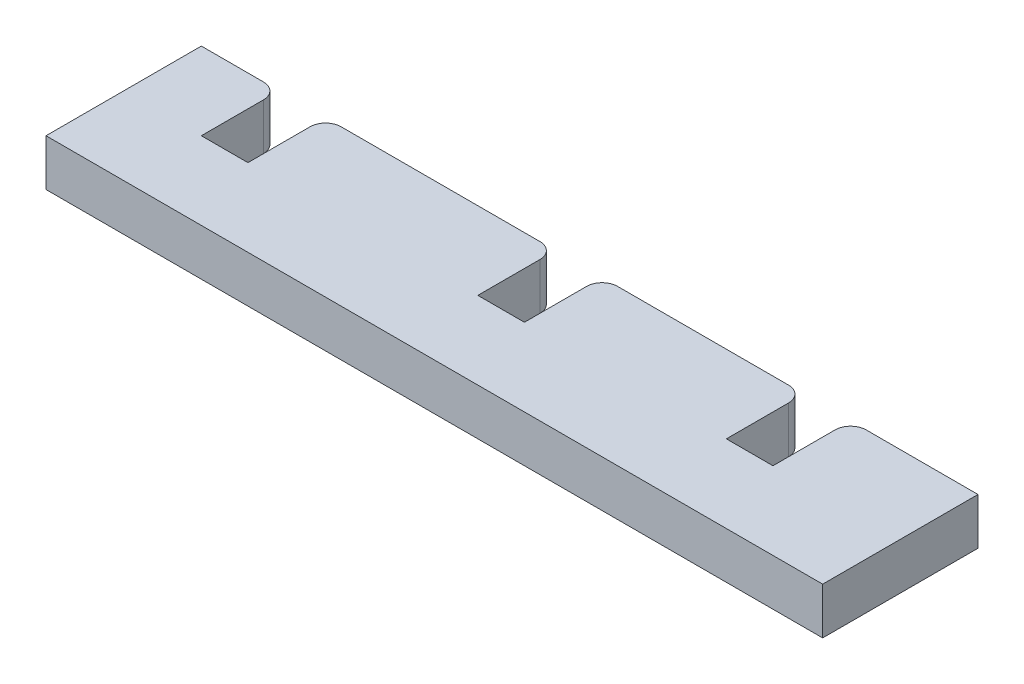
SolidWorks part; units mm, degrees
ref_plane "Front Plane" through (0, 0, 0) normal (0, 0, 1) x (1, 0, 0)
ref_plane "Top Plane" through (0, 0, 0) normal (0, 1, 0) x (1, 0, 0)
ref_plane "Right Plane" through (0, 0, 0) normal (1, 0, 0) x (0, 0, -1)
sketch "Sketch1" plane through (0, 0, 0) normal (0, 0, 1) x (1, 0, 0)
  line L1 (0, 0) -> (50, 0)
  line L2 (0, 0) -> (0, 3)
  line L3 (0, 3) -> (50, 3)
  line L4 (50, 0) -> (50, 3)
  dimension "D1" = 3
  dimension "D2" = 50
extrude "Boss-Extrude1" add sketch "Sketch1" along normal blind 10
sketch "Sketch3" plane through (0, 0, 0) normal (0, 0, -1) x (-1, 0, 0)
  line L0 (0, 0) -> (-50, 0) construction
  line L4 (-82.8, 3) -> (-82.8, 0)
  line L5 (-50, 3) -> (0, 3) construction
  line L7 (-79.8, 3) -> (-79.8, 0)
  line L9 (-61.8, 3) -> (-61.8, 0)
  line L10 (-82.8, 3) -> (-79.8, 3)
  line L12 (-58.8, 3) -> (-58.8, 0)
  line L14 (-41.8, 3) -> (-41.8, 0)
  line L16 (-38.8, 3) -> (-38.8, 0)
  line L18 (-25.8, 3) -> (-25.8, 0)
  line L20 (-22.8, 3) -> (-22.8, 0)
  line L22 (-8, 3) -> (-8, 0)
  line L24 (-5, 3) -> (-5, 0)
  line L27 (-5, 0) -> (-8, 0)
  line L28 (-79.8, 0) -> (-82.8, 0)
  line L29 (-61.8, 3) -> (-58.8, 3)
  line L30 (-41.8, 3) -> (-38.8, 3)
  line L31 (-58.8, 0) -> (-61.8, 0)
  line L32 (-38.8, 0) -> (-41.8, 0)
  line L33 (-25.8, 3) -> (-22.8, 3)
  line L34 (-8, 3) -> (-5, 3)
  line L35 (-22.8, 0) -> (-25.8, 0)
  line L36 (0, 3) -> (0, 0) construction
  dimension "D2" = 3
  dimension "D3" = 18
  dimension "D4" = 3
  dimension "D5" = 17
  dimension "D6" = 3
  dimension "D7" = 13
  dimension "D8" = 3
  dimension "D9" = 14.8
  dimension "D10" = 3
  dimension "D11" = 5
extrude "Cut-Extrude2" cut sketch "Sketch3" against normal blind 5
fillet "Fillet2" radius 1 6 edges at (5, 1.5, 0) (8, 1.5, 0) (22.8, 1.5, 0) (25.8, 1.5, 0) (38.8, 1.5, 0) (41.8, 1.5, 0)
